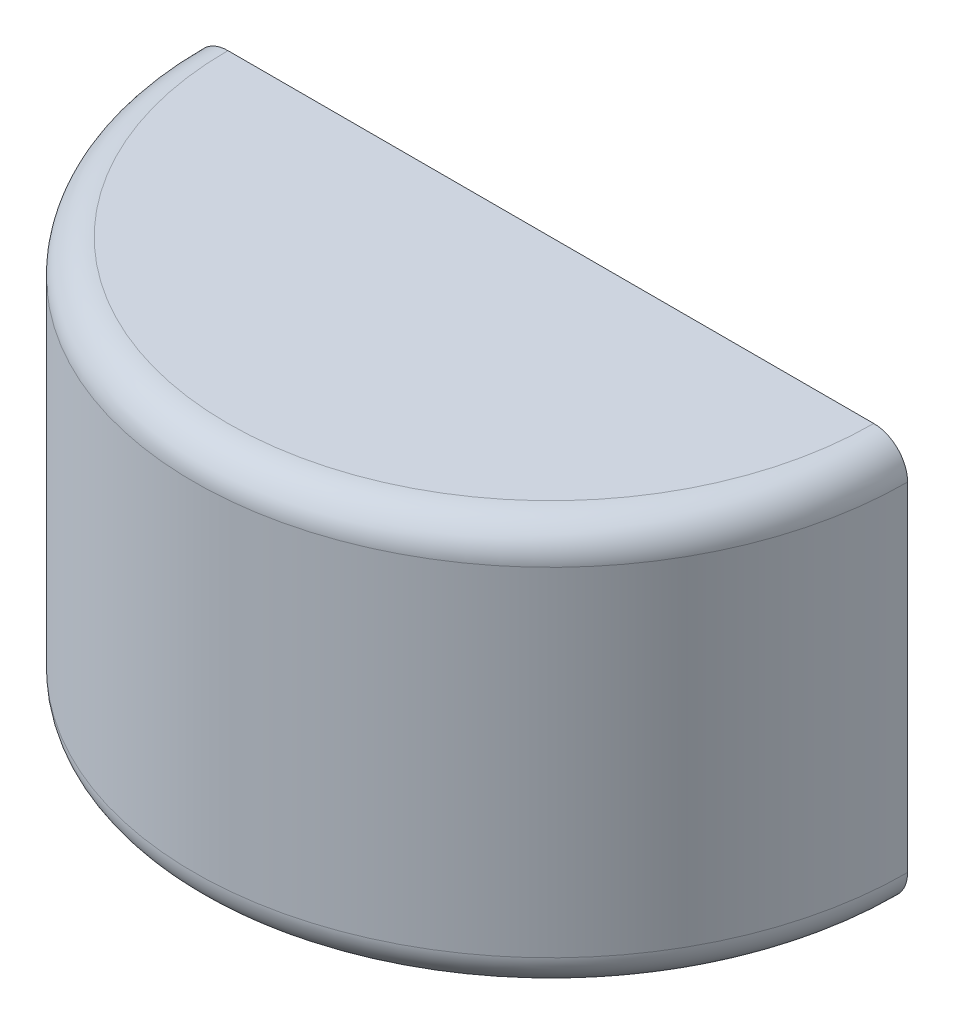
SolidWorks part; units mm, degrees
material "Custom Plastic"
ref_plane "Front Plane" through (0, 0, 0) normal (0, 0, 1) x (1, 0, 0)
ref_plane "Top Plane" through (0, 0, 0) normal (0, 1, 0) x (1, 0, 0)
ref_plane "Right Plane" through (0, 0, 0) normal (1, 0, 0) x (0, 0, -1)
sketch "Sketch1" plane through (0, 0, 0) normal (0, 0, 1) x (1, 0, 0)
  line L0 (0, 0) -> (0, 152.4) construction
  line L2 (0, 0) -> (-133.985, 0)
  line L3 (0, 0) -> (0, 152.4)
  line L4 (0, 152.4) -> (-133.985, 152.4)
  line L5 (-133.985, 0) -> (-133.985, 152.4)
  dimension "D1" = 152.4
  dimension "D2" = 133.985
revolve "Revolve1" add sketch "Sketch1" angle 180 about L0
fillet "Fillet1" radius 12.7 2 edges at (0, 0, 133.985) (0, 152.4, 133.985)
